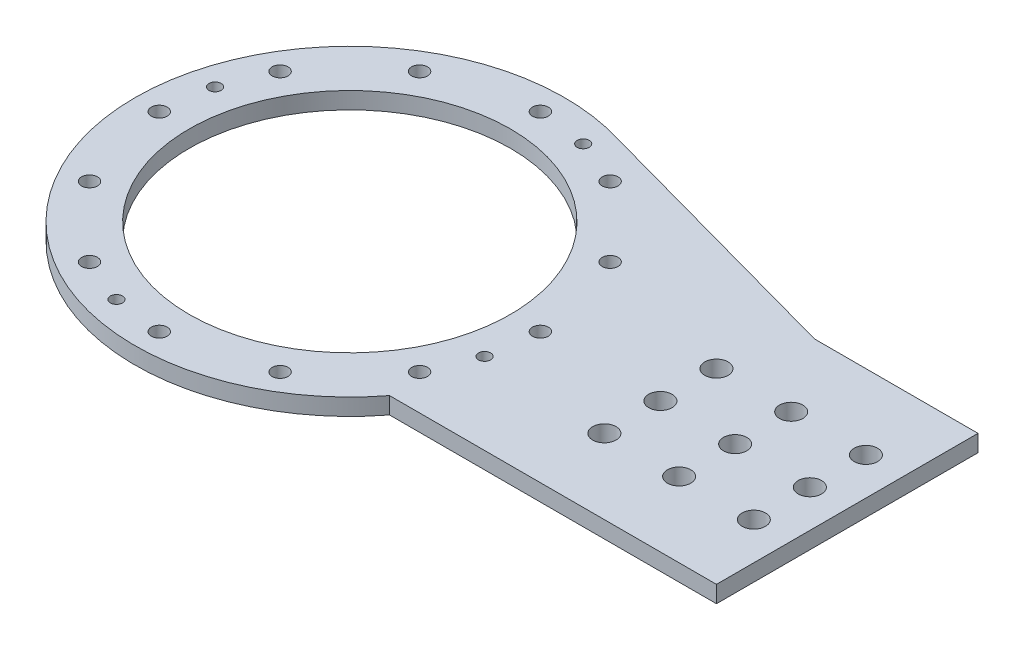
SolidWorks part; units mm, degrees
ref_plane "Front Plane" through (0, 0, 0) normal (0, 0, 1) x (1, 0, 0)
ref_plane "Top Plane" through (0, 0, 0) normal (0, 1, 0) x (1, 0, 0)
ref_plane "Right Plane" through (0, 0, 0) normal (1, 0, 0) x (0, 0, -1)
sketch "Sketch1" plane through (0, 0, 0) normal (0, 1, 0) x (1, 0, 0)
  circle A0 centre (0, 0) radius 57.5
  dimension "D1" = 115
extrude "Boss-Extrude1" add sketch "Sketch1" along normal blind 4.5
sketch "Sketch2" plane through (0, 0, 0) normal (0, 1, 0) x (1, 0, 0)
  line L0 (133.1258, 35) -> (-6.8742, 35)
  line L1 (133.1258, 35) -> (133.1258, -35)
  line L2 (-6.8742, 35) -> (-6.8742, -35)
  line L3 (133.1258, -35) -> (-6.8742, -35)
  line L4 (-6.8742, 0) -> (133.1258, 0) construction
  line L5 (63.1258, 35) -> (63.1258, -35) construction
  point P1 (63.1258, 0)
  dimension "D1" = 70
  dimension "D2" = 140
extrude "Boss-Extrude2" add sketch "Sketch2" along normal blind 4.5
sketch "Sketch3" plane through (0, 0, 0) normal (0, 1, 0) x (1, 0, 0)
  line L0 (89.3733, 35) -> (13.7685, 55.8272)
  line L1 (133.1258, 35) -> (45.6207, 35) construction
  line L2 (13.7685, 55.8272) -> (13.7685, 13.5588)
  line L3 (13.7685, 13.5588) -> (89.3733, 35)
  circle A0 centre (0, 0) radius 57.5 construction
extrude "Boss-Extrude3" add sketch "Sketch3" along normal blind 4.5
mirror "Mirror1" [suppressed] about plane through (0, 0, 0) normal (0, 0, 1)
sketch "Sketch4" plane through (0, 4.5, 0) normal (0, 1, 0) x (1, 0, 0)
  circle A0 centre (0, 0) radius 43
  dimension "D1" = 86
extrude "Cut-Extrude1" cut sketch "Sketch4" against normal through all
sketch "Sketch7" plane through (0, 4.5, 0) normal (0, 1, 0) x (1, 0, 0)
  line L0 (0, 0) -> (133.1258, 0) construction
  line L1 (133.1258, -35) -> (133.1258, 35) construction
  line L2 (123.1258, 15) -> (123.1258, -15) construction
  circle A0 centre (123.1258, 15) radius 3.125
  circle A1 centre (123.1258, -15) radius 3.125
  point P8 (123.1258, 0)
  dimension "D1" = 6.25
  dimension "D2" = 30
  dimension "D3" = 10
extrude "Cut-Extrude8" cut sketch "Sketch7" against normal through all
pattern_linear "LPattern1" count 3 spacing 20 along (-1, 0, 0) of "Cut-Extrude8"
sketch "Sketch5" plane through (0, 0, 0) normal (0, 1, 0) x (1, 0, 0)
  circle A0 centre (0, 0) radius 51 construction
  circle A1 centre (-51, 0) radius 2.125
  dimension "D1" = 4.25
  dimension "D2" = 102
extrude "Cut-Extrude5" cut sketch "Sketch5" against normal through all and the other way through all contours A1
pattern_circular "CirPattern1" count 12 over 360 about axis through (0, 0, 0) along (0, 1, 0) of "Cut-Extrude5"
sketch "Sketch11" plane through (0, 4.5, 0) normal (0, 1, 0) x (1, 0, 0)
  line L0 (52.9426, -35) -> (62.7348, -25.9656)
  line L1 (45.6207, -35) -> (133.1258, -35) construction
  line L2 (62.7348, -25.9656) -> (71.0702, -35)
  line L3 (71.0702, -35) -> (52.9426, -35)
extrude "Cut-Extrude16" [suppressed] cut sketch "Sketch11" against normal through all
sketch "Sketch12" plane through (0, 4.5, 0) normal (0, 1, 0) x (1, 0, 0)
  line L0 (0, 0) -> (-51, 0) construction
  line L1 (0, 0) -> (-49.2622, 13.1998) construction
  circle A0 centre (0, 0) radius 51 construction
  circle A1 centre (-49.2622, 13.1998) radius 1.625
  dimension "D1" = 102
  dimension "D2" = 3.25
  dimension "D3" = 15
extrude "Cut-Extrude17" cut sketch "Sketch12" against normal through all
pattern_circular "CirPattern2" count 4 over 360 about axis through (0, 0, 0) along (0, 1, 0) of "Cut-Extrude17"
sketch "Sketch13" plane through (0, 4.5, 0) normal (0, 1, 0) x (1, 0, 0)
  line L0 (133.1258, 0) -> (0, 0) construction
  line L1 (133.1258, -35) -> (133.1258, 35) construction
  circle A0 centre (123.1258, 0) radius 3.125
  dimension "D1" = 6.25
  dimension "D2" = 10
extrude "Cut-Extrude18" cut sketch "Sketch13" against normal blind 10 contours A0
pattern_linear "LPattern2" count 3 spacing 20 along (-1, 0, 0) of "Cut-Extrude18"
